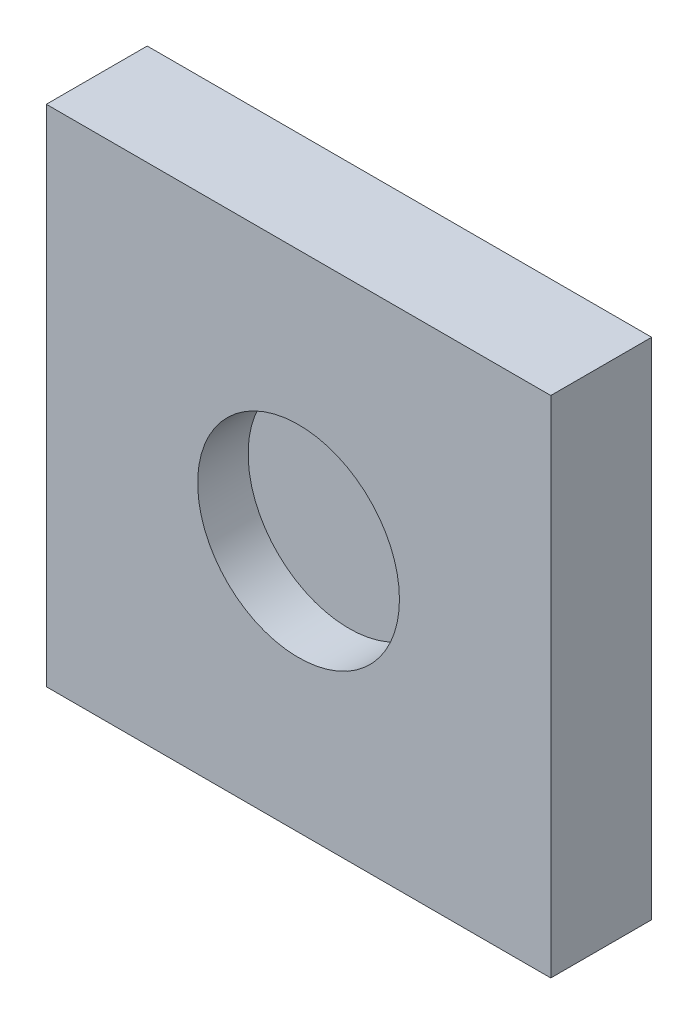
SolidWorks part; units mm, degrees
ref_plane "Front Plane" through (0, 0, 0) normal (0, 0, 1) x (1, 0, 0)
ref_plane "Top Plane" through (0, 0, 0) normal (0, 1, 0) x (1, 0, 0)
ref_plane "Right Plane" through (0, 0, 0) normal (1, 0, 0) x (0, 0, -1)
sketch "Sketch2" plane through (0, 0, 0) normal (0, 0, 1) x (1, 0, 0)
  line L1 (50, 50) -> (-50, 50)
  line L2 (50, 50) -> (50, -50)
  line L3 (50, -50) -> (-50, -50)
  line L4 (-50, 50) -> (-50, -50)
  line L5 (50, 50) -> (-50, -50) construction
  line L6 (50, -50) -> (-50, 50) construction
  point P0 (0, 0)
  dimension "D1" = 100
  dimension "D2" = 100
extrude "Boss-Extrude1" add sketch "Sketch2" along normal blind 20 contours L2 L1 L4 L3
sketch "Sketch3" plane through (0, 0, 20) normal (0, 0, 1) x (1, 0, 0)
  circle A0 centre (0, 0) radius 20
extrude "Cut-Extrude1" cut sketch "Sketch3" against normal blind 10
